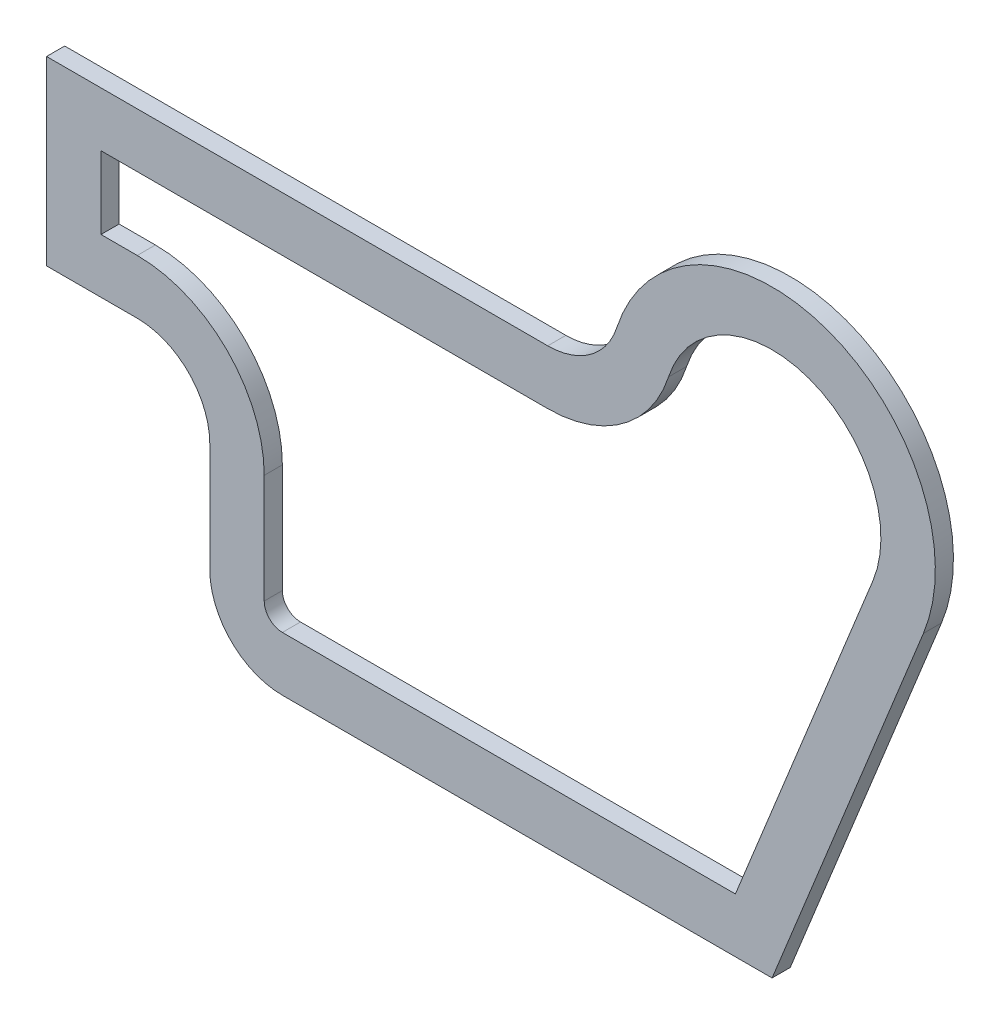
SolidWorks part; units mm, degrees
ref_plane "Front Plane" through (0, 0, 0) normal (0, 0, 1) x (1, 0, 0)
ref_plane "Top Plane" through (0, 0, 0) normal (0, 1, 0) x (1, 0, 0)
ref_plane "Right Plane" through (0, 0, 0) normal (1, 0, 0) x (0, 0, -1)
sketch "Sketch1" plane through (0, 0, 0) normal (0, 0, 1) x (1, 0, 0)
  line L0 (41.7161, -16.875) -> (0, -120)
  line L1 (-200, 0) -> (0, 0)
  line L2 (-200, 0) -> (-200, -120)
  line L3 (-200, -120) -> (0, -120)
  line L4 (0, 0) -> (0, -120)
  line L5 (-200, -50) -> (-155, -50)
  line L6 (-155, -50) -> (-155, -120)
  circle A0 centre (0, 0) radius 45
  circle A1 centre (-175, -70) radius 20
  circle A2 centre (-135, -100) radius 20
  circle A3 centre (-61.8466, 20) radius 20
  point P15 (135.3661, 82.2371)
  point P16 (305.4031, 127.6284)
  point P17 (328.459, 116.8209)
  point P18 (0, 0)
  point P20 (-84.9637, 19.4914)
  point P21 (-126.5969, -51.3698)
  point P22 (-116.8489, -125.7631)
  point P23 (-133.6878, -66.432)
  point P24 (0, 0)
  point P25 (0, 0)
  point P26 (0, 0)
  point P27 (0, 0)
  point P28 (0, 0)
  point P29 (0, 0)
  point P30 (0, 0)
  dimension "D2" = 45
  dimension "D3" = 20
  dimension "D4" = 20
  dimension "D5" = 20
  dimension "D1" = 200
  dimension "D6" = 45
  dimension "D7" = 50
  dimension "D8" = 120
extrude "Boss-Extrude1" add sketch "Sketch1" along normal blind 5 contours A2 L3 L4 A0 L1 L2 L5 L6 | A3 L1 A0 | A2 | A1 L6 L5 | A0 L4 L0 | L4 A0 L1
sketch "Sketch2" plane through (0, 0, 5) normal (0, 0, 1) x (1, 0, 0)
  line L1 (-61.8466, -15) -> (-185, -15)
  line L2 (-185, -15) -> (-185, -35)
  line L3 (-185, -35) -> (-175, -35)
  line L4 (-140, -70) -> (-140, -100)
  line L5 (-135, -105) -> (-10.113, -105)
  line L6 (-10.113, -105) -> (27.8107, -11.25)
  line L7 (-61.8466, 0) -> (-200, 0)
  line L8 (-200, 0) -> (-200, -50)
  line L9 (-200, -50) -> (-175, -50)
  line L10 (-155, -70) -> (-155, -100)
  line L11 (-135, -120) -> (0, -120)
  line L12 (0, -120) -> (41.7161, -16.875)
  line L13 (-61.8466, 0) -> (-200, 0)
  line L14 (-200, 0) -> (-200, -50)
  line L15 (-200, -50) -> (-175, -50)
  line L16 (-155, -70) -> (-155, -100)
  line L17 (-135, -120) -> (0, -120)
  line L18 (0, -120) -> (41.7161, -16.875)
  arc A0 (-140, -70) -> (-175, -35) centre (-175, -70) ccw
  arc A1 (-140, -100) -> (-135, -105) centre (-135, -100) ccw
  arc A2 (27.8107, -11.25) -> (-28.5446, 9.2308) centre (0, 0) ccw
  arc A3 (-61.8466, -15) -> (-28.5446, 9.2308) centre (-61.8466, 20) ccw
  arc A4 (41.7161, -16.875) -> (-42.8169, 13.8462) centre (0, 0) ccw
  arc A5 (-61.8466, 0) -> (-42.8169, 13.8462) centre (-61.8466, 20) ccw
  arc A6 (-155, -70) -> (-175, -50) centre (-175, -70) ccw
  arc A7 (-155, -100) -> (-135, -120) centre (-135, -100) ccw
  arc A8 (41.7161, -16.875) -> (-42.8169, 13.8462) centre (0, 0) ccw
  arc A9 (-61.8466, 0) -> (-42.8169, 13.8462) centre (-61.8466, 20) ccw
  arc A10 (-155, -70) -> (-175, -50) centre (-175, -70) ccw
  arc A11 (-155, -100) -> (-135, -120) centre (-135, -100) ccw
  dimension "D2" = 15
extrude "Cut-Extrude1" cut sketch "Sketch2" against normal through all contours A3 A2 L6 L5 A1 L4 A0 L3 L2 L1
equation "\"filletRad\" = 20"
equation "\"rectHeight\"= 120"
equation "\"rectLength\"= 200"
equation "\"bigCircle\"= 45'radius"
equation "\"smallRectHeight\"= 50"
equation "\"smallRectLength\"= 45"
equation "\"D1@Sketch1\"=\"rectLength\""
equation "\"D2@Sketch1\"=\"bigCircle\""
equation "\"D3@Sketch1\"=\"filletRad\""
equation "\"D5@Sketch1\"=\"filletRad\""
equation "\"D6@Sketch1\"=\"smallRectLength\""
equation "\"D7@Sketch1\"=\"smallRectHeight\""
equation "\"D4@Sketch1\"=\"filletRad\""
equation "\"D8@Sketch1\"=\"rectHeight\""
equation "\"material\"= 5"
equation "\"offsetWidth\"= \"material\" * 3"
equation "\"D2@Sketch2\"=\"offsetWidth\""
equation "\"D1@Boss-Extrude1\"=\"material\""
